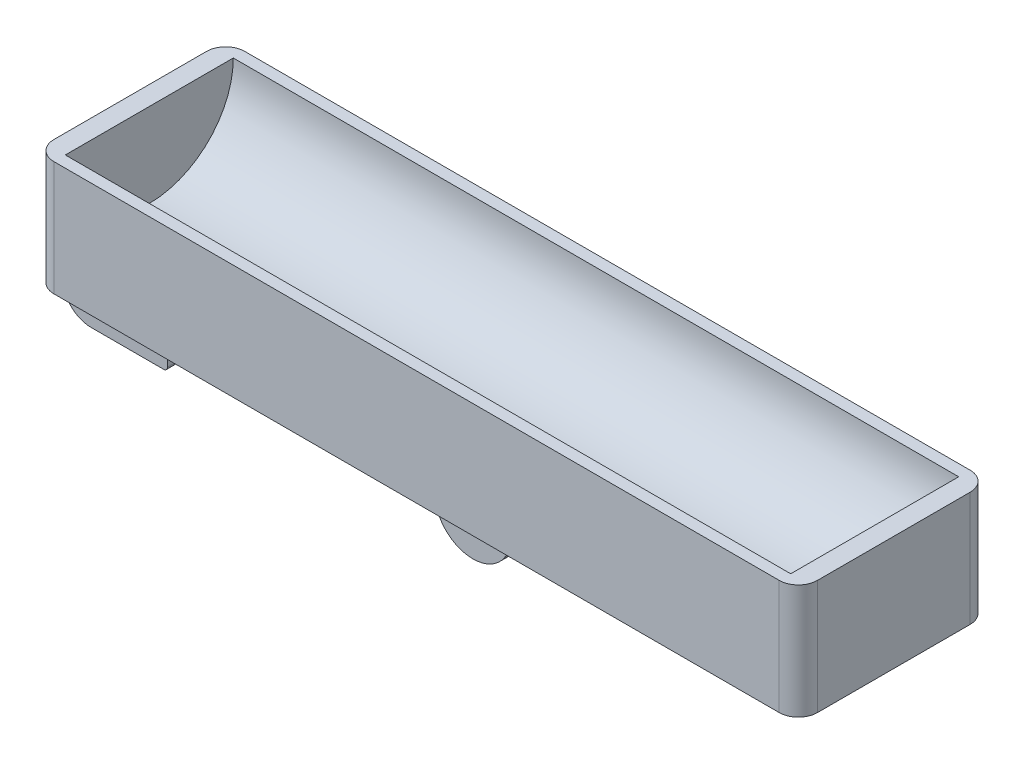
SolidWorks part; units mm, degrees
ref_plane "Front Plane" through (0, 0, 0) normal (0, 0, 1) x (1, 0, 0)
ref_plane "Top Plane" through (0, 0, 0) normal (0, 1, 0) x (1, 0, 0)
ref_plane "Right Plane" through (0, 0, 0) normal (1, 0, 0) x (0, 0, -1)
sketch "Sketch2" plane through (0, 0, 0) normal (1, 0, 0) x (0, 0, -1)
  line L1 (-25, -15) -> (25, -15)
  line L2 (-25, -15) -> (-25, 15)
  line L3 (-25, 15) -> (25, 15)
  line L4 (25, -15) -> (25, 15)
  line L5 (-25, -15) -> (25, 15) construction
  line L6 (-25, 15) -> (25, -15) construction
  point P0 (0, 0)
  dimension "D1" = 50
  dimension "D2" = 30
extrude "Boss-Extrude2" add sketch "Sketch2" along normal blind 100
sketch "Sketch3" plane through (0, 0, 0) normal (-1, 0, 0) x (0, 0, 1)
  line L0 (-25, -15) -> (-25, 15)
  line L1 (-25, 15) -> (-22, 15)
  line L2 (-25, 15) -> (25, 15) construction
  line L3 (22, 15) -> (25, 15)
  line L4 (25, 15) -> (25, -15)
  line L5 (25, -15) -> (-25, -15)
  arc A0 (-22, 15) -> (22, 15) centre (0, 15) ccw
  line M10 (25, 15) -> (-25, 15)
  dimension "D1" = 22
extrude "Cut-Extrude1" cut sketch "Sketch3" against normal blind 95 contours A0 M10
mirror "Mirror7" about plane through (0, 0, 0) normal (1, 0, 0) of "Boss-Extrude2", "Cut-Extrude1"
sketch "Sketch4" plane through (0, -15, 0) normal (0, -1, 0) x (1, 0, 0)
  line L0 (0, -5.25) -> (0, 0) construction
  line L7 (-10, -10.25) -> (10, -10.25)
  line L8 (-10, -10.25) -> (-10, -5.25)
  line L9 (-10, -5.25) -> (10, -5.25)
  line L10 (10, -10.25) -> (10, -5.25)
  line L11 (-10, -10.25) -> (10, -5.25) construction
  line L12 (-10, -5.25) -> (10, -10.25) construction
  point P0 (10, -10.25)
  point P3 (0, 0)
  point P5 (0, -7.75)
  dimension "D1" = 20
  dimension "D2" = 5
  dimension "D3" = 5.25
extrude "Boss-Extrude3" add sketch "Sketch4" along normal blind 10
sketch "Sketch5" plane through (0, 0, -10.25) normal (0, 0, -1) x (-1, 0, 0)
  line L0 (-10, -25) -> (10, -25)
  arc A0 (-10, -25) -> (10, -25) centre (0, -25) ccw
  dimension "D1" = 10
extrude "Boss-Extrude4" add sketch "Sketch5" against normal up to surface (5 mm away) up to face at (0, -20, -5.25)
sketch "Sketch6" plane through (0, 0, -10.25) normal (0, 0, -1) x (-1, 0, 0)
  circle A0 centre (0, -25) radius 2.55
  point P2 (14.2176, -27.3057)
  point P3 (0, -25)
  dimension "D1" = 5.1
extrude "Cut-Extrude2" cut sketch "Sketch6" against normal up to surface (5 mm away) up to face at (0, -22.5, -5.25)
mirror "Mirror12" about plane through (0, 0, 0) normal (0, 0, 1) of "Cut-Extrude2", "Boss-Extrude4", "Boss-Extrude3"
sketch "Sketch9" plane through (0, 0, -10.25) normal (0, 0, -1) x (-1, 0, 0)
  line L0 (0, -25) -> (100, -25) construction
  line L6 (-100, -15) -> (100, -15) construction
  line L11 (80, -15) -> (95, -15)
  line L13 (100, -17.5) -> (95, -17.5)
  line L14 (95, -17.5) -> (95, -15)
  line L15 (100, -32.5) -> (80, -32.5)
  line L16 (80, -32.5) -> (80, -15)
  circle A0 centre (100, -25) radius 2.55
  arc A3 (100, -17.5) -> (100, -32.5) centre (100, -25) cw
  point P5 (79.5324, -30.1)
  dimension "D1" = 5.1
  dimension "D2" = 15
  dimension "D3" = 15
  dimension "D4" = 20
extrude "Boss-Extrude6" add sketch "Sketch9" against normal blind 5
mirror "Mirror13" about plane through (0, 0, 0) normal (0, 0, 1) of "Boss-Extrude6"
fillet "Fillet1" radius 5 4 edges at (100, 0, 25) (100, 0, -25) (-100, 0, -25) (-100, 0, 25)
fillet "Fillet3" radius 1 18 edges at (-87.5, -15, 5.25) (-80, -15, 7.75) (-95, -15, 7.75) (-87.5, -15, 10.25) (-95, -15, -7.75) (-87.5, -15, -5.25) (-80, -15, -7.75) (-87.5, -15, -10.25) (0, -15, 10.25) (-10, -15, 7.75) (0, -15, 5.25) (10, -15, 7.75) (0, -15, -5.25) (10, -15, -7.75) (-10, -15, -7.75) (0, -15, -10.25) (-80, -32.5, 7.75) (-80, -32.5, -7.75)
